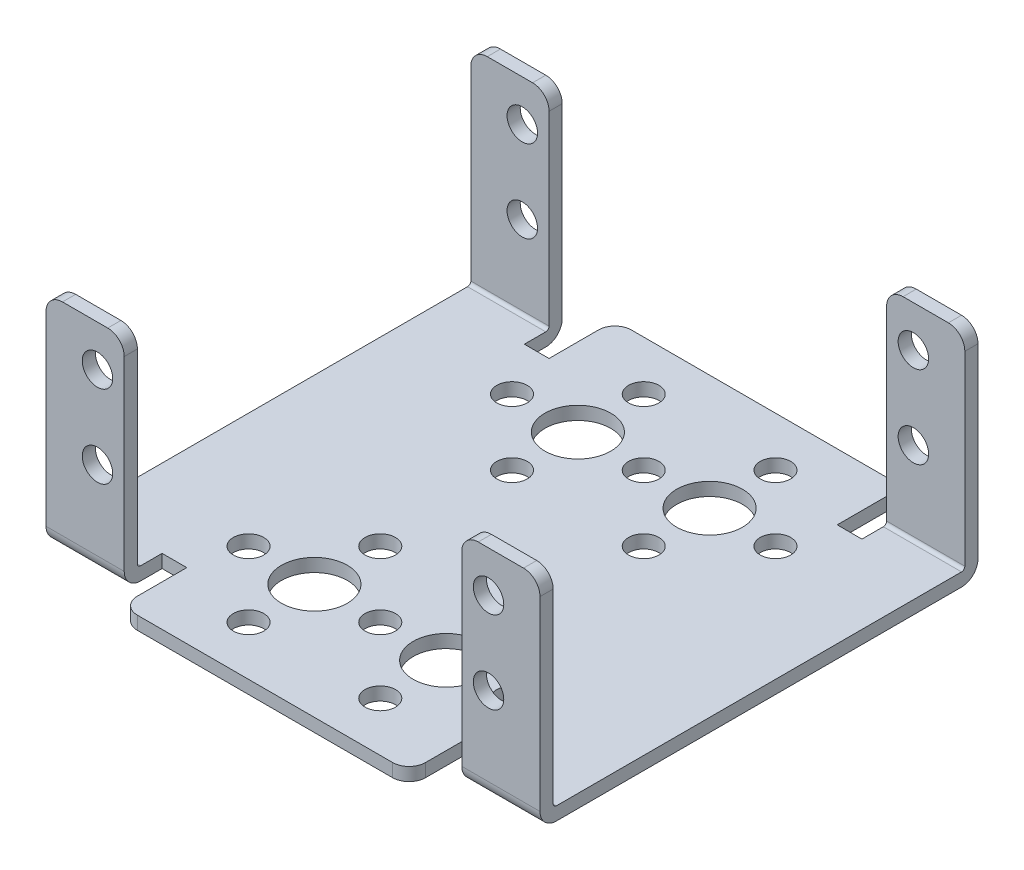
SolidWorks part; units mm, degrees
material "2024 Alloy"
ref_plane "Front Plane" through (0, 0, 0) normal (0, 0, 1) x (1, 0, 0)
ref_plane "Top Plane" through (0, 0, 0) normal (0, 1, 0) x (1, 0, 0)
ref_plane "Right Plane" through (0, 0, 0) normal (1, 0, 0) x (0, 0, -1)
ref_plane "Plane1" through (60, 0, 0) normal (1, 0, 0) x (0, 0, -1)
sketch "Sketch1" plane through (60, 0, 0) normal (1, 0, 0) x (0, 0, -1)
  line L0 (53.2, 0) -> (53.2, 26.6)
  line L1 (53.2, 26.6) -> (0, 26.6)
  line L2 (0, 26.6) -> (0, 0)
  line L3 (0, 0) -> (53.2, 0)
extrude "Boss-Extrude1" add sketch "Sketch1" against normal blind 9.5
sketch "Sketch2" plane through (50.5, 0, 0) normal (-1, 0, 0) x (0, 0, 1)
  line L0 (-1.6, 26.6) -> (-51.6, 26.6)
  line L1 (-51.6, 26.6) -> (-51.6, 1.6)
  line L2 (-51.6, 1.6) -> (-1.6, 1.6)
  line L3 (-1.6, 1.6) -> (-1.6, 26.6)
extrude "Cut-Extrude1" cut sketch "Sketch2" against normal through all
sketch "Sketch3" plane through (50.5, 0, 0) normal (-1, 0, 0) x (0, 0, 1)
  line L0 (-48.6, 1.6) -> (-4.6, 1.6)
  line L1 (-4.6, 1.6) -> (-4.6, 0)
  line L2 (-4.6, 0) -> (-48.6, 0)
  line L3 (-48.6, 0) -> (-48.6, 1.6)
extrude "Boss-Extrude2" add sketch "Sketch3" along normal blind 50.5
sketch "Sketch4" plane through (0, 0, -48.6) normal (0, 0, -1) x (-1, 0, 0)
  line L0 (0, 1.6) -> (0, 0)
  line L1 (0, 0) -> (-9.5, 0)
  line L2 (-9.5, 0) -> (-9.5, 1.6)
  line L3 (-9.5, 1.6) -> (0, 1.6)
extrude "Boss-Extrude3" add sketch "Sketch4" along normal blind 4.6
sketch "Sketch5" plane through (0, 1.6, 0) normal (0, 1, 0) x (-1, 0, 0)
  line L0 (-9.5, -51.6) -> (0, -51.6)
  line L1 (0, -51.6) -> (0, -53.2)
  line L2 (0, -53.2) -> (-9.5, -53.2)
  line L3 (-9.5, -53.2) -> (-9.5, -51.6)
extrude "Boss-Extrude4" add sketch "Sketch5" along normal blind 25
sketch "Sketch6" plane through (0, 0, -4.6) normal (0, 0, 1) x (1, 0, 0)
  line L0 (9.5, 1.6) -> (9.5, 0)
  line L1 (9.5, 0) -> (0, 0)
  line L2 (0, 0) -> (0, 1.6)
  line L3 (0, 1.6) -> (9.5, 1.6)
extrude "Boss-Extrude5" add sketch "Sketch6" along normal blind 4.6
sketch "Sketch7" plane through (0, 1.6, 0) normal (0, 1, 0) x (-1, 0, 0)
  line L0 (0, -1.6) -> (-9.5, -1.6)
  line L1 (-9.5, -1.6) -> (-9.5, 0)
  line L2 (-9.5, 0) -> (0, 0)
  line L3 (0, 0) -> (0, -1.6)
extrude "Boss-Extrude6" add sketch "Sketch7" along normal blind 25
sketch "Sketch8" plane through (0, 0, -48.6) normal (0, 0, -1) x (-1, 0, 0)
  line L0 (-12.5, 0) -> (-47.5, 0)
  line L1 (-47.5, 0) -> (-47.5, 1.6)
  line L2 (-47.5, 1.6) -> (-12.5, 1.6)
  line L3 (-12.5, 1.6) -> (-12.5, 0)
extrude "Boss-Extrude7" add sketch "Sketch8" along normal blind 8
sketch "Sketch9" plane through (0, 0, -4.6) normal (0, 0, 1) x (1, 0, 0)
  line L0 (12.5, 1.6) -> (47.5, 1.6)
  line L1 (47.5, 1.6) -> (47.5, 0)
  line L2 (47.5, 0) -> (12.5, 0)
  line L3 (12.5, 0) -> (12.5, 1.6)
extrude "Boss-Extrude8" add sketch "Sketch9" along normal blind 8
hole_wizard "Ø8.0 (8) Diameter Hole1" positions "Sketch11" profile "Sketch10" hole size "Ø8.0" standard "ANSI Metric"
sketch "Sketch11" plane through (0, 0, 0) normal (0, -1, 0) x (-1, 0, 0)
  point P0 (-22, 42.6)
  point P1 (-22, 10.6)
  point P2 (-38, 42.6)
  point P3 (-38, 10.6)
sketch "Sketch10" plane through (22, 0, -42.6) normal (1, 0, 0) x (0, 0, -1)
  line L0 (0, 0) -> (0, 26.6)
  line L1 (0, 26.6) -> (4, 26.6)
  line L2 (4, 26.6) -> (4, 0)
  line L5 (4, 0) -> (0, 0)
  line L11 (0, -6.35) -> (0, 107.95) construction
  dimension "Thru Hole Dia." = 8
  dimension "Thru Hole Depth" = 26.6
hole_wizard "Ø3.7 (3.7) Diameter Hole1" positions "Sketch13" profile "Sketch12" hole size "Ø3.7" standard "ANSI Metric"
sketch "Sketch13" plane through (0, 0, 0) normal (0, -1, 0) x (-1, 0, 0)
  point P0 (-30, 42.6)
  point P1 (-22, 18.6)
  point P2 (-14, 10.6)
  point P3 (-22, 2.6)
  point P4 (-22, 50.6)
  point P5 (-14, 42.6)
  point P6 (-22, 34.6)
  point P7 (-38, 18.6)
  point P8 (-46, 10.6)
  point P9 (-38, 2.6)
  point P10 (-38, 50.6)
  point P11 (-46, 42.6)
  point P12 (-38, 34.6)
  point P13 (-30, 10.6)
sketch "Sketch12" plane through (30, 0, -42.6) normal (1, 0, 0) x (0, 0, -1)
  line L0 (0, 0) -> (0, 26.6)
  line L1 (0, 26.6) -> (1.85, 26.6)
  line L2 (1.85, 26.6) -> (1.85, 0)
  line L5 (1.85, 0) -> (0, 0)
  line L11 (0, -6.35) -> (0, 107.95) construction
  dimension "Thru Hole Dia." = 3.7
  dimension "Thru Hole Depth" = 26.6
hole_wizard "Ø3.7 (3.7) Diameter Hole2" positions "Sketch15" profile "Sketch14" hole size "Ø3.7" standard "ANSI Metric"
sketch "Sketch15" plane through (0, 0, -53.2) normal (0, 0, -1) x (-1, 0, 0)
  point P0 (-53.75, 11.6)
  point P1 (-53.75, 21.6)
  point P2 (-6.25, 11.6)
  point P3 (-6.25, 21.6)
sketch "Sketch14" plane through (53.75, 11.6, -53.2) normal (1, 0, 0) x (0, 1, 0)
  line L0 (0, 0) -> (0, 1.6)
  line L1 (0, 1.6) -> (1.85, 1.6)
  line L2 (1.85, 1.6) -> (1.85, 0)
  line L5 (1.85, 0) -> (0, 0)
  line L11 (0, -6.35) -> (0, 107.95) construction
  dimension "Thru Hole Dia." = 3.7
  dimension "Thru Hole Depth" = 1.6
hole_wizard "Ø3.7 (3.7) Diameter Hole3" positions "Sketch17" profile "Sketch16" hole size "Ø3.7" standard "ANSI Metric"
sketch "Sketch17" plane through (0, 0, 0) normal (0, 0, 1) x (1, 0, 0)
  point P0 (53.75, 11.6)
  point P1 (53.75, 21.6)
  point P2 (6.25, 11.6)
  point P3 (6.25, 21.6)
sketch "Sketch16" plane through (53.75, 11.6, 0) normal (1, 0, 0) x (0, -1, 0)
  line L0 (0, 0) -> (0, 56.6)
  line L1 (0, 56.6) -> (1.85, 56.6)
  line L2 (1.85, 56.6) -> (1.85, 0)
  line L5 (1.85, 0) -> (0, 0)
  line L11 (0, -6.35) -> (0, 107.95) construction
  dimension "Thru Hole Dia." = 3.7
  dimension "Thru Hole Depth" = 56.6
fillet "Fillet1" radius 0.4 4 edges at (4.75, 1.6, -51.6) (55.25, 1.6, -1.6) (4.75, 1.6, -1.6) (55.25, 1.6, -51.6)
fillet "Fillet2" radius 2 16 edges at (4.75, 0, 0) (4.75, 0, -53.2) (55.25, 0, -53.2) (47.5, 0.8, 3.4) (60, 26.6, -0.8) (12.5, 0.8, -56.6) (50.5, 26.6, -52.4) (12.5, 0.8, 3.4) (60, 26.6, -52.4) (55.25, 0, 0) (0, 26.6, -52.4) (47.5, 0.8, -56.6) (9.5, 26.6, -52.4) (9.5, 26.6, -0.8) (0, 26.6, -0.8) (50.5, 26.6, -0.8)
